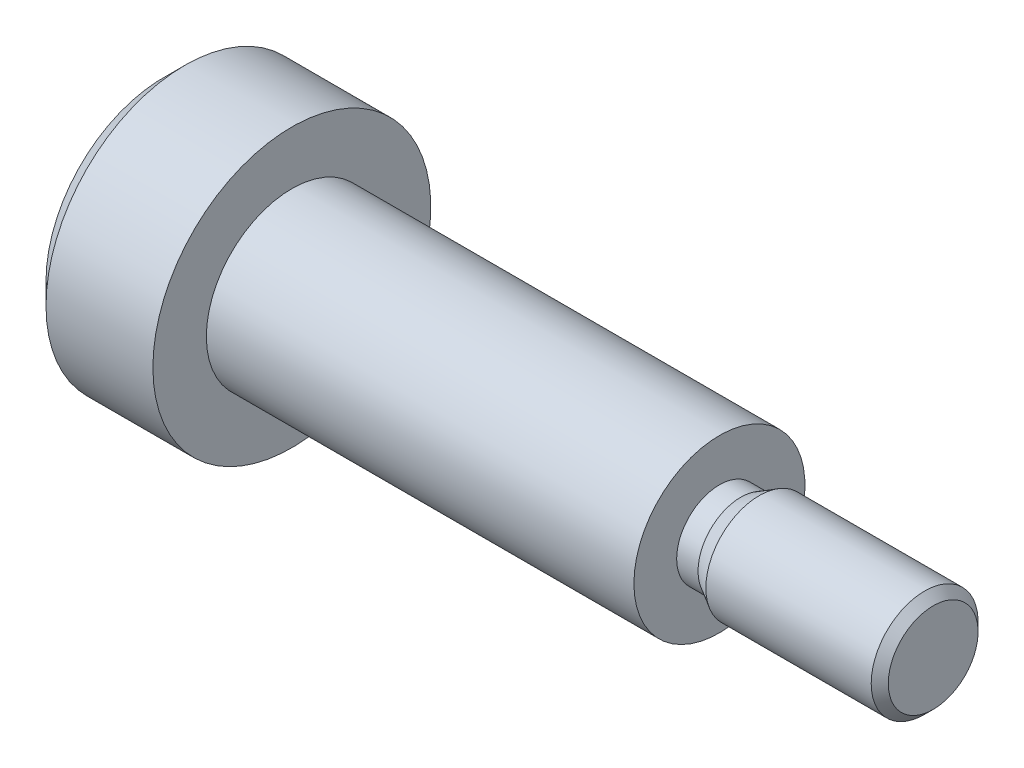
SolidWorks part; units mm, degrees
ref_plane "Vorne" through (0, 0, 0) normal (0, 0, 1) x (1, 0, 0)
ref_plane "Oben" through (0, 0, 0) normal (0, 1, 0) x (1, 0, 0)
ref_plane "Rechts" through (0, 0, 0) normal (1, 0, 0) x (0, 0, -1)
sketch "Skizze1" plane through (0, 0, 0) normal (0, 0, 1) x (1, 0, 0)
  line L0 (0, 0) -> (51.1181, 0) construction
  line L1 (0, 0) -> (0, 3.25)
  line L2 (0, 3.25) -> (3, 3.25)
  line L3 (3, 3.25) -> (3, 2)
  line L4 (3, 2) -> (13, 2)
  line L5 (13, 2) -> (13, 1.25)
  line L6 (13, 1.25) -> (18, 1.25)
  line L7 (18, 1.25) -> (18, 0)
  line L8 (18, 0) -> (0, 0)
  dimension "D1" = 2.5
  dimension "D2" = 4
  dimension "D3" = 6.5
  dimension "D4" = 3
  dimension "D5" = 10
  dimension "D6" = 5
revolve "Rotation1" add sketch "Skizze1" angle 360 about L0
chamfer "Fase1" distance 0.5 angle 45 1 edges at (0, 0, 3.25)
chamfer "Fase2" distance 0.2 angle 45 1 edges at (18, 0, 1.25)
sketch "Skizze2" plane through (0, 0, 0) normal (0, 0, 1) x (1, 0, 0)
  line L0 (13, 1.25) -> (13, 1)
  line L1 (13, -1.25) -> (13, 1.25) construction
  line L2 (13, 1) -> (13.5, 1)
  line L3 (13.5, 1) -> (13.933, 1.25)
  line L4 (17.8, 1.25) -> (13, 1.25) construction
  line L5 (13.933, 1.25) -> (13, 1.25)
  line L6 (0, 0) -> (18.8631, 0) construction
  dimension "D1" = 2
  dimension "D2" = 30
  dimension "D3" = 0.5
revolve "Schnitt-Rotation1" cut sketch "Skizze2" angle 360 about L6
move or copy body "Körper-Verschieben/Kopieren1" [suppressed] bodies to move or copy 104
